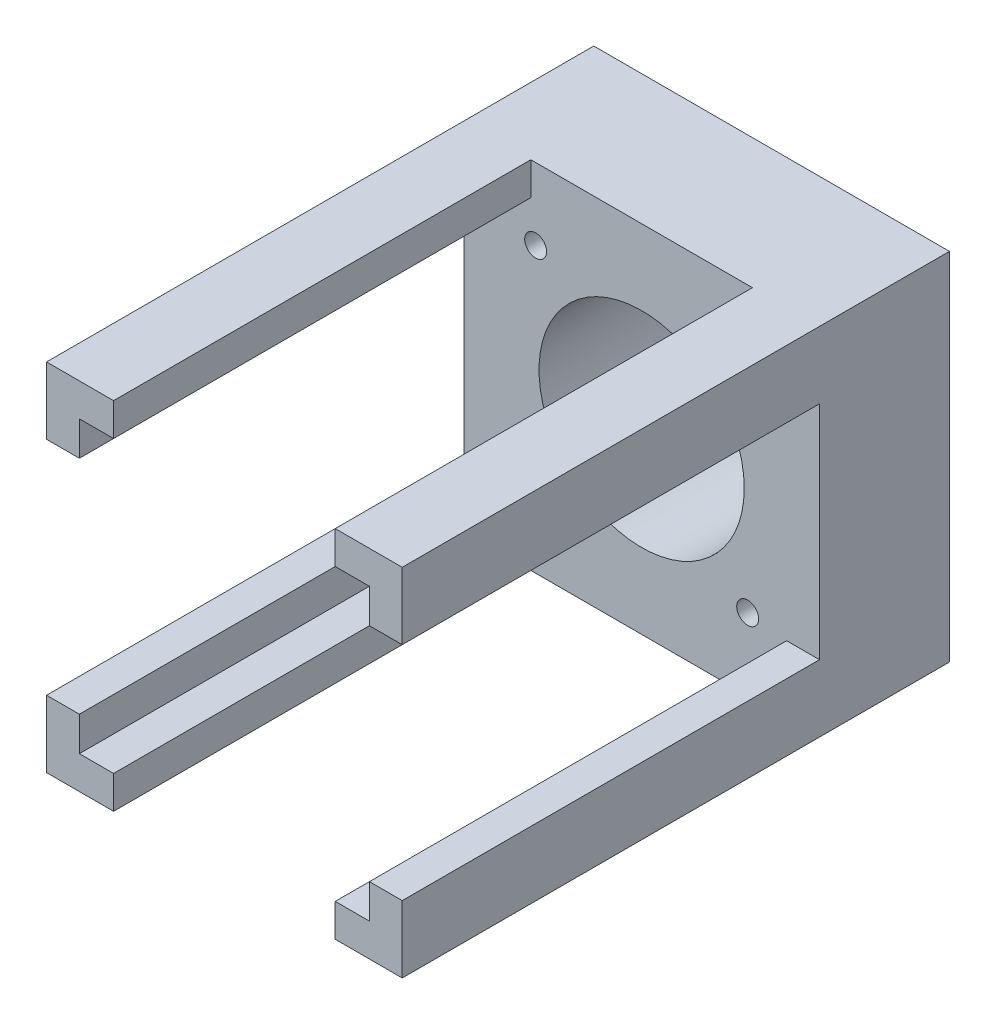
SolidWorks part; units mm, degrees
ref_plane "前视基准面" through (0, 0, 0) normal (0, 0, 1) x (1, 0, 0)
ref_plane "上视基准面" through (0, 0, 0) normal (0, 1, 0) x (1, 0, 0)
ref_plane "右视基准面" through (0, 0, 0) normal (1, 0, 0) x (0, 0, -1)
sketch "草图1" plane through (0, 0, 0) normal (0, 0, 1) x (1, 0, 0)
  line L0 (4.3544, 8.8386) -> (35.3544, -22.1614) construction
  line L1 (4.3544, 8.8386) -> (35.3544, 8.8386) construction
  line L2 (4.3544, 8.8386) -> (4.3544, -22.1614) construction
  line L3 (4.3544, -22.1614) -> (35.3544, -22.1614) construction
  line L4 (35.3544, 8.8386) -> (35.3544, -22.1614) construction
  line L5 (-6.1456, 19.3386) -> (-6.1456, -32.6614)
  line L6 (-1.1456, 14.3386) -> (40.8544, 14.3386) construction
  line L7 (-1.1456, 14.3386) -> (-1.1456, -27.6614) construction
  line L8 (-1.1456, -27.6614) -> (40.8544, -27.6614) construction
  line L9 (40.8544, 14.3386) -> (40.8544, -27.6614) construction
  line L10 (-6.1456, -32.6614) -> (45.8544, -32.6614)
  line L11 (45.8544, 19.3386) -> (45.8544, -32.6614)
  line L12 (-6.1456, 19.3386) -> (45.8544, 19.3386)
  circle A0 centre (19.8544, -6.6614) radius 15
  circle A1 centre (35.3544, 8.8386) radius 1.6
  circle A2 centre (35.3544, -22.1614) radius 1.6
  circle A3 centre (4.3544, -22.1614) radius 1.6
  circle A4 centre (4.3544, 8.8386) radius 1.6
  point P14 (19.8544, 14.3386)
  point P15 (19.8544, 8.8386)
  point P16 (40.8544, -6.6614)
  point P17 (35.3544, -6.6614)
  dimension "D3" = 3.2
  dimension "D4" = 30
  dimension "D1" = 31
  dimension "D2" = 31
  dimension "D5" = 42
  dimension "D6" = 42
  dimension "D7" = 5
extrude "凸台-拉伸1" add sketch "草图1" along normal blind 80
sketch "草图2" plane through (0, 0, 80) normal (0, 0, 1) x (1, 0, 0)
  line L0 (-1.3456, 14.5386) -> (-1.3456, 9.5386)
  line L1 (-6.1456, 19.3386) -> (45.8544, 19.3386)
  line L2 (-6.1456, 19.3386) -> (-6.1456, -32.6614)
  line L3 (-6.1456, -32.6614) -> (45.8544, -32.6614)
  line L4 (45.8544, 19.3386) -> (45.8544, -32.6614)
  line L5 (-1.3456, -27.8614) -> (3.6544, -27.8614)
  line L6 (41.0544, 14.5386) -> (41.0544, 9.5386)
  line L7 (-1.3456, 14.5386) -> (3.6544, 14.5386)
  line L9 (-6.1456, 9.5386) -> (-1.3456, 9.5386)
  line L10 (-6.1456, 9.5386) -> (-6.1456, -22.8614)
  line L11 (-6.1456, -22.8614) -> (-1.3456, -22.8614)
  line L13 (3.6544, 19.3386) -> (36.0544, 19.3386)
  line L14 (3.6544, 19.3386) -> (3.6544, 14.5386)
  line L16 (36.0544, 19.3386) -> (36.0544, 14.5386)
  line L17 (-6.1456, -6.6614) -> (-1.3456, -6.6614) construction
  line L19 (36.0544, -32.6614) -> (36.0544, -27.8614)
  line L20 (3.6544, -32.6614) -> (36.0544, -32.6614)
  line L21 (3.6544, -32.6614) -> (3.6544, -27.8614)
  line L22 (45.8544, -22.8614) -> (41.0544, -22.8614)
  line L24 (45.8544, 9.5386) -> (41.0544, 9.5386)
  line L25 (45.8544, 9.5386) -> (45.8544, -22.8614)
  line L26 (-1.3456, -22.8614) -> (-1.3456, -27.8614)
  line L27 (-1.3456, 14.5386) -> (-1.3456, -27.8614) construction
  line L28 (36.0544, -27.8614) -> (41.0544, -27.8614)
  line L29 (36.0544, 14.5386) -> (41.0544, 14.5386)
  line L30 (-1.3456, 14.5386) -> (41.0544, 14.5386) construction
  line L31 (41.0544, -22.8614) -> (41.0544, -27.8614)
  line L32 (41.0544, 14.5386) -> (41.0544, -27.8614) construction
  line L33 (-1.3456, -27.8614) -> (41.0544, -27.8614) construction
  circle M23 centre (19.8544, -6.6614) radius 15
  circle M24 centre (35.3544, 8.8386) radius 1.6
  circle M25 centre (35.3544, -22.1614) radius 1.6
  circle M26 centre (4.3544, -22.1614) radius 1.6
  circle M27 centre (4.3544, 8.8386) radius 1.6
  dimension "D2" = 5
  dimension "D3" = 5
  dimension "D4" = 5
  dimension "D5" = 5
  dimension "D1" = 4.8
extrude "切除-拉伸1" cut sketch "草图2" against normal blind 61 contours L31 L22 L4 L24 L6 L29 L16 L1 L14 L7 L0 L9 L2 L11 L26 L5 L21 L3 L19 L28 M23 M25 M27 M26 M24
